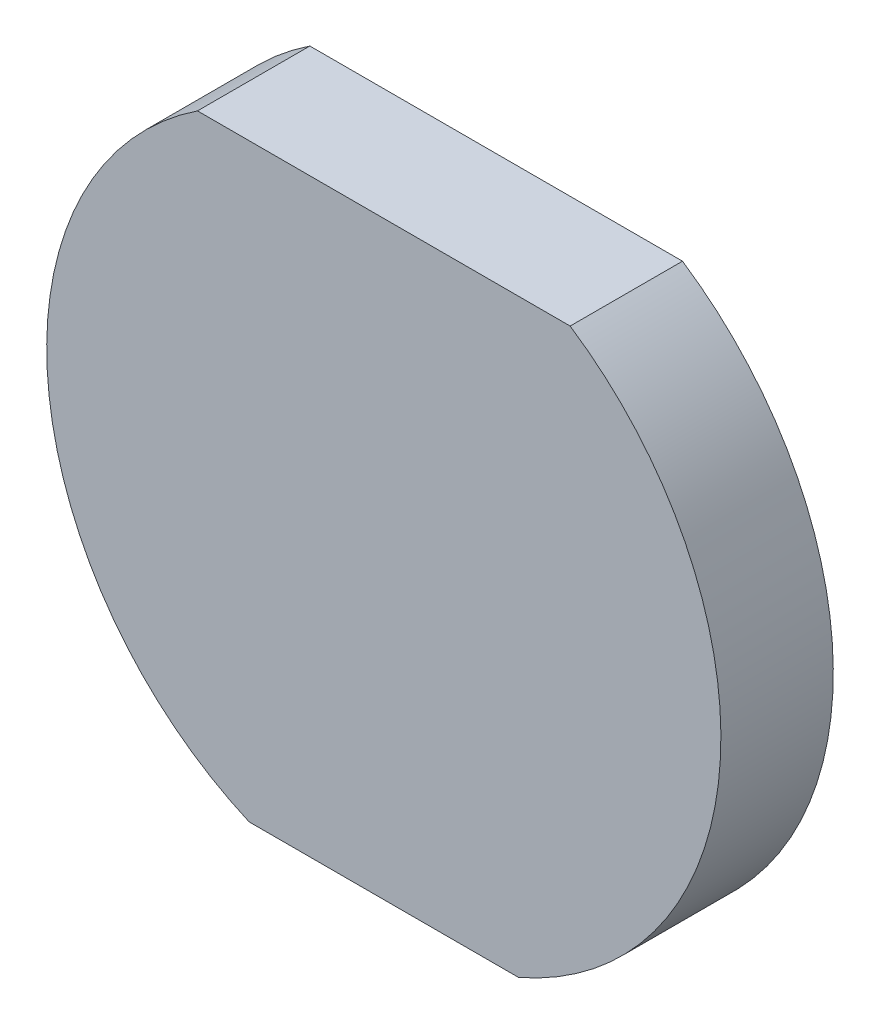
SolidWorks part; units mm, degrees
ref_plane "Front Plane" through (0, 0, 0) normal (0, 0, 1) x (1, 0, 0)
ref_plane "Top Plane" through (0, 0, 0) normal (0, 1, 0) x (1, 0, 0)
ref_plane "Right Plane" through (0, 0, 0) normal (1, 0, 0) x (0, 0, -1)
sketch "Sketch1" plane through (0, 0, 0) normal (0, 0, 1) x (1, 0, 0)
  circle A0 centre (0, 0) radius 6
  dimension "D1" = 12
extrude "Boss-Extrude1" add sketch "Sketch1" along normal blind 2
sketch "Sketch2" plane through (0, 0, 2) normal (0, 0, 1) x (1, 0, 0)
  line L0 (-3.3166, 5) -> (3.3166, 5)
  line L1 (2.3979, -5.5) -> (-2.3979, -5.5)
  circle A0 centre (0, 0) radius 6 construction
  arc A1 (3.3166, 5) -> (-3.3166, 5) centre (0, 0) ccw
  arc A2 (-2.3979, -5.5) -> (2.3979, -5.5) centre (0, 0) ccw
  circle M1 centre (0, 0) radius 6
  dimension "D1" = 5
  dimension "D2" = 5.5
extrude "Cut-Extrude1" cut sketch "Sketch2" against normal blind 2 contours L0 M1 | L1 M1
